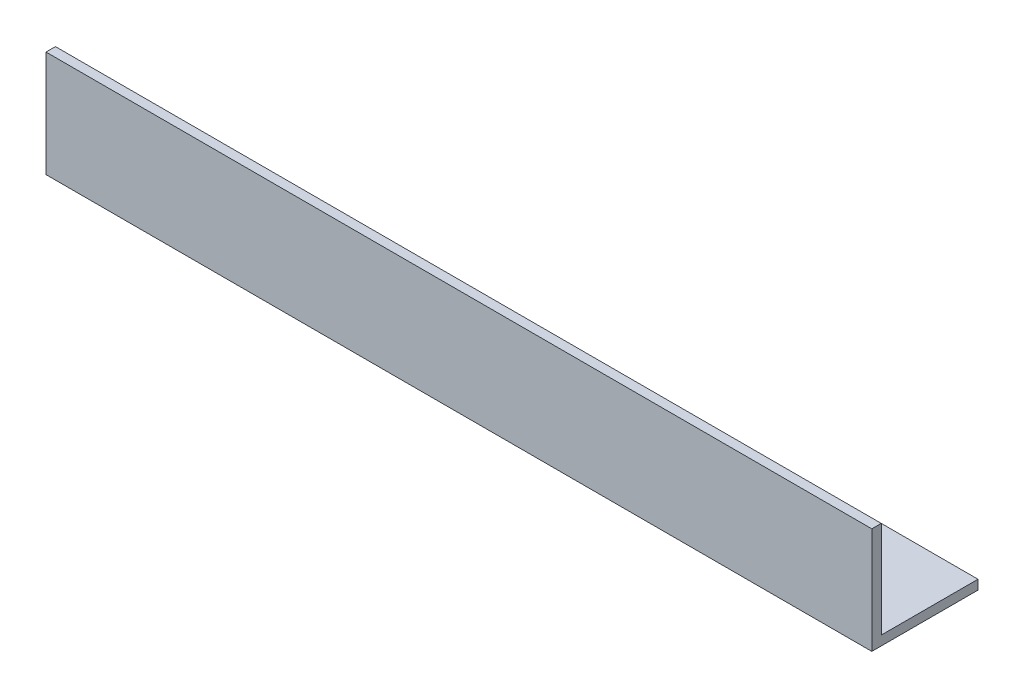
SolidWorks part; units mm, degrees
ref_plane "Спереди" through (0, 0, 0) normal (0, 0, 1) x (1, 0, 0)
ref_plane "Сверху" through (0, 0, 0) normal (0, 1, 0) x (1, 0, 0)
ref_plane "Справа" through (0, 0, 0) normal (1, 0, 0) x (0, 0, -1)
sketch "Эскиз1" plane through (0, 0, 0) normal (1, 0, 0) x (0, 0, -1)
  line L0 (0, 45) -> (0, 0)
  line L1 (0, 0) -> (45, 0)
extrude "Вытянуть-Тонкостенный1" add sketch "Эскиз1" along normal blind 350 thin thin type one direction reverse wall 4
